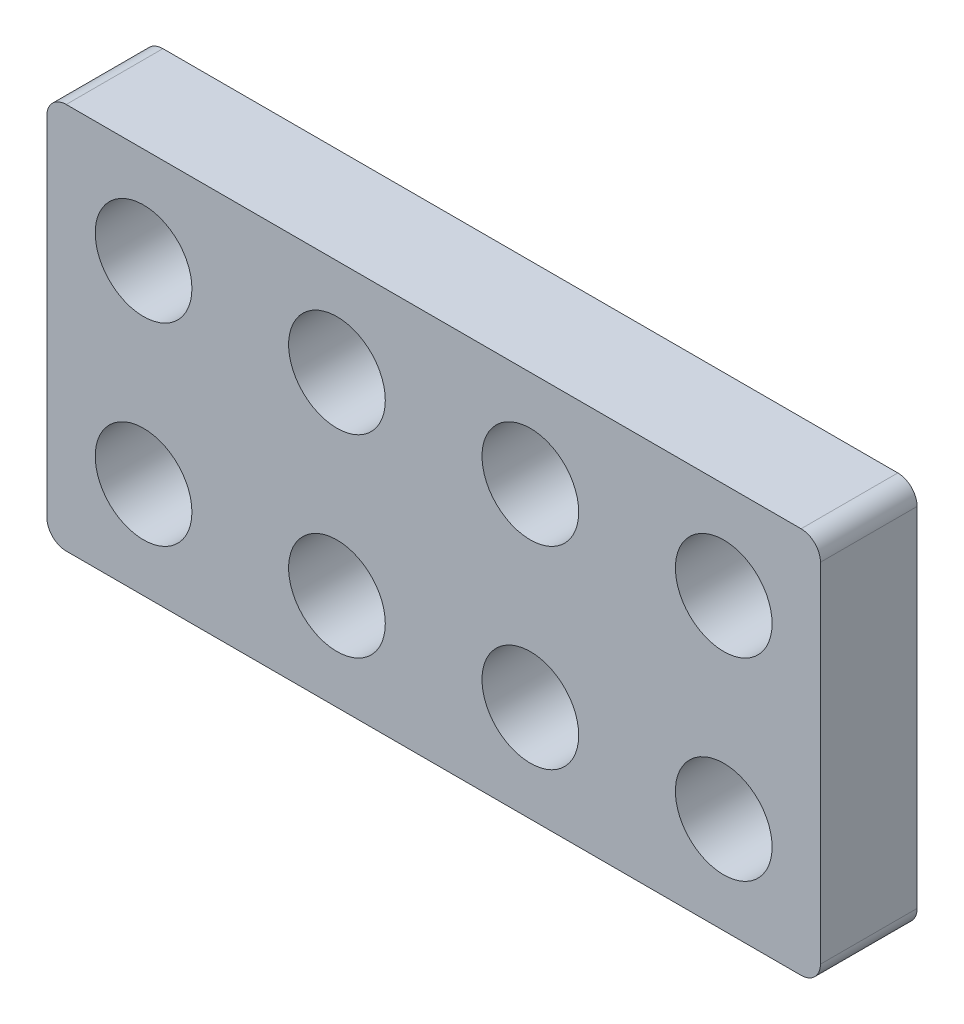
SolidWorks part; units mm, degrees
ref_plane "Front Plane" through (0, 0, 0) normal (0, 0, 1) x (1, 0, 0)
ref_plane "Top Plane" through (0, 0, 0) normal (0, 1, 0) x (1, 0, 0)
ref_plane "Right Plane" through (0, 0, 0) normal (1, 0, 0) x (0, 0, -1)
sketch "Sketch2" plane through (0, 0, 0) normal (0, 0, 1) x (1, 0, 0)
  line L1 (0, 0) -> (80, 0)
  line L2 (0, 0) -> (0, 40)
  line L3 (0, 40) -> (80, 40)
  line L4 (80, 0) -> (80, 40)
  dimension "D1" = 80
  dimension "D2" = 40
extrude "Boss-Extrude2" add sketch "Sketch2" along normal blind 10
sketch "Sketch3" plane through (0, 0, 10) normal (0, 0, 1) x (1, 0, 0)
  circle A0 centre (10, 10) radius 5
  point P5 (0, 6.6062)
  point P8 (9.3982, 6.5175)
  dimension "D3" = 10
  dimension "D1" = 10
  dimension "D2" = 10
extrude "Cut-Extrude1" cut sketch "Sketch3" against normal through all contours A0
pattern_linear "LPattern2" count 4 spacing 20 along (1, 0, 0) count 2 spacing 20 along (0, 1, 0) of "Cut-Extrude1"
fillet "Fillet1" radius 2 4 edges at (80, 40, 5) (80, 0, 5) (0, 0, 5) (0, 40, 5)
